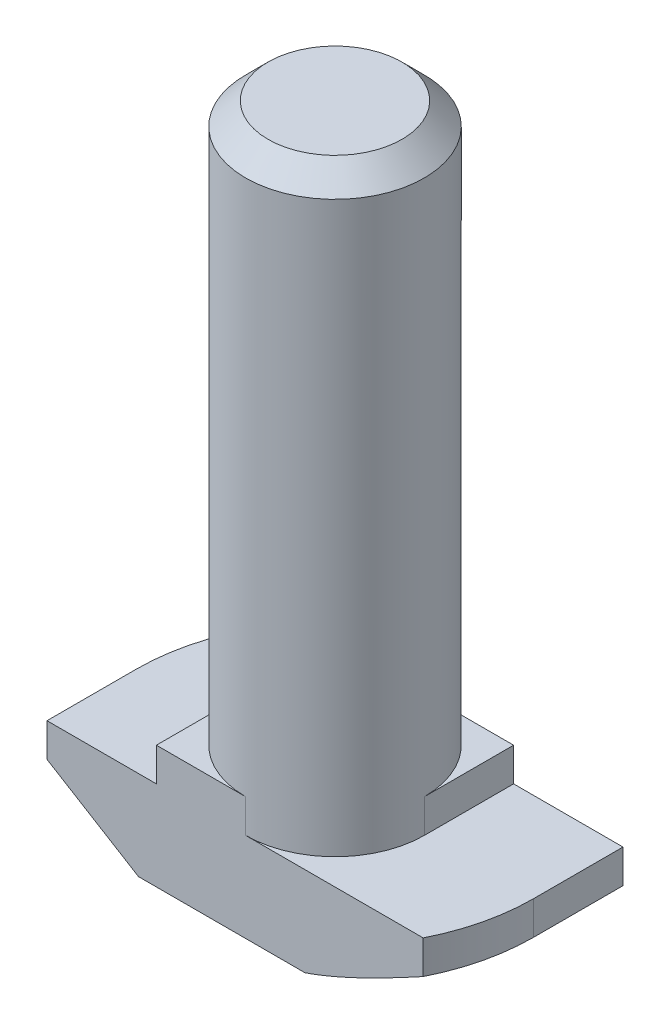
SolidWorks part; units mm, degrees
ref_plane "Спереди" through (0, 0, 0) normal (0, 0, 1) x (1, 0, 0)
ref_plane "Сверху" through (0, 0, 0) normal (0, 1, 0) x (1, 0, 0)
ref_plane "Справа" through (0, 0, 0) normal (1, 0, 0) x (0, 0, -1)
sketch "Эскиз1" plane through (0, 0, 0) normal (0, 0, 1) x (1, 0, 0)
  line L0 (8.9, 0) -> (-8.9, 0)
  line L1 (-8.9, 0) -> (-8.9, 4)
  line L2 (-8.9, 4) -> (-4, 4)
  line L3 (-4, 4) -> (-4, 5.5)
  line L4 (-4, 5.5) -> (4, 5.5)
  line L5 (0, 5.5) -> (0, 0) construction
  line L6 (4, 4) -> (4, 5.5)
  line L7 (8.9, 4) -> (4, 4)
  line L8 (8.9, 0) -> (8.9, 4)
  point P12 (-8.25, 2.6435)
  point P13 (-4, 3.6993)
  dimension "D1" = 8
  dimension "D2" = 17.8
  dimension "D3" = 5.5
  dimension "D4" = 1.5
extrude "Бобышка-Вытянуть1" add sketch "Эскиз1" along normal mid plane 8
sketch "Эскиз3" plane through (0, 5.5, 0) normal (0, 1, 0) x (1, 0, 0)
  line L1 (4, 4) -> (-4, 4) construction
  line L2 (-4, 0) -> (-4, 4)
  line L3 (-4, 4) -> (0, 4)
  line L4 (0, -4) -> (4, -4)
  line L5 (4, -4) -> (-4, -4) construction
  line L6 (4, -4) -> (4, 0)
  line L7 (4, -4) -> (4, 4) construction
  arc A0 (-4, 0) -> (0, 4) centre (0, 0) cw
  arc A1 (4, 0) -> (0, -4) centre (0, 0) cw
extrude "Вырез-Вытянуть1" cut sketch "Эскиз3" against normal up to surface (1.5 mm away) up to face at (-6.45, 4, 0)
sketch "Эскиз2" plane through (0, 5.5, 0) normal (0, 1, 0) x (1, 0, 0)
  circle A0 centre (0, 0) radius 4
  dimension "D1" = 8
extrude "Бобышка-Вытянуть2" add sketch "Эскиз2" along normal blind 25
cosmetic thread "Условное изображение резьбы1" parameters "D1"=25, "D2"=6.619
sketch "Эскиз4" plane through (0, 4, 0) normal (0, 1, 0) x (1, 0, 0)
  line L0 (-8.9, -4) -> (-8.9, 4) construction
  line L1 (8.9, -4) -> (8.9, 4) construction
  line L2 (-7.9505, 4) -> (-8.9, 4)
  line L3 (-8.9, 4) -> (-8.9, 0)
  line L4 (7.9505, -4) -> (8.9, -4)
  line L5 (8.9, -4) -> (8.9, 0)
  arc A0 (-8.9, 0) -> (-7.9505, 4) centre (0, 0) cw
  arc A1 (8.9, 0) -> (7.9505, -4) centre (0, 0) cw
extrude "Вырез-Вытянуть2" cut sketch "Эскиз4" against normal through all
sketch "Эскиз5" plane through (0, 0, 4) normal (0, 0, 1) x (1, 0, 0)
  line L0 (-8.9, 2.5) -> (-4.8, 0)
  line L1 (-8.9, 4) -> (-8.9, 0) construction
  line L2 (-8.9, 0) -> (7.9505, 0) construction
  line L3 (-4.8, 0) -> (-8.9, 0)
  line L4 (-8.9, 0) -> (-8.9, 2.5)
  line L6 (-4, 4) -> (-8.9, 4) construction
  line L7 (-4, 5.5) -> (-4, 4) construction
  point P6 (-4.9519, 0)
  point P9 (0, 0)
  point P10 (-4.6154, 0)
  point P12 (-8.25, 2.2665)
  point P15 (0, 0)
  dimension "D1" = 1.5
  dimension "D2" = 0.8
sketch "Эскиз6" plane through (0, 0, 0) normal (0, -1, 0) x (1, 0, 0)
  line L0 (0, -8.9) -> (8.9, -8.9)
  line L1 (8.9, -8.9) -> (8.9, 0)
  line L2 (0, 8.9) -> (-8.9, 8.9)
  line L3 (-8.9, 8.9) -> (-8.9, 0)
  arc A0 (-8.9, 0) -> (0, -8.9) centre (0, 0) ccw
  arc A1 (8.9, 0) -> (0, 8.9) centre (0, 0) ccw
  point P10 (0, 0)
sweep "Вырез-По траектории1" cut profiles "Эскиз5" path "Эскиз6"
chamfer "Фаска2" distance 1 angle 45 1 edges at (0, 30.5, 4)
